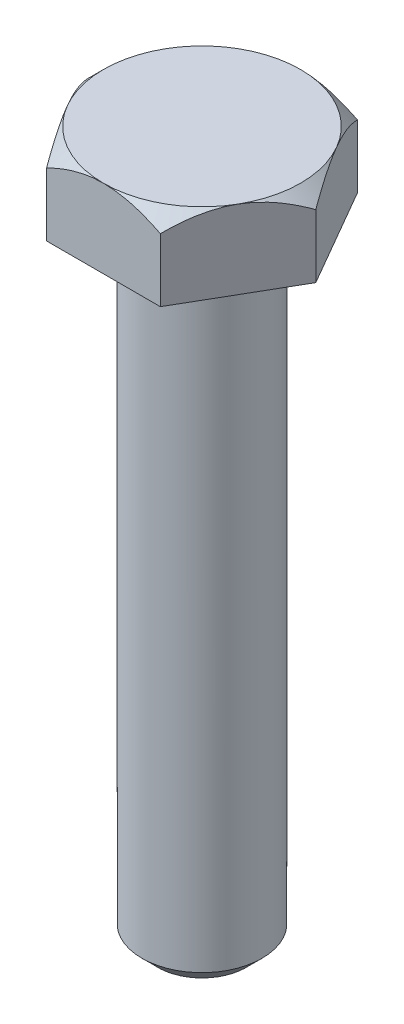
SolidWorks part; units mm, degrees
ref_plane "Спереди" through (0, 0, 0) normal (0, 0, 1) x (1, 0, 0)
ref_plane "Сверху" through (0, 0, 0) normal (0, 1, 0) x (1, 0, 0)
ref_plane "Справа" through (0, 0, 0) normal (1, 0, 0) x (0, 0, -1)
sketch "Эскиз6" plane through (0, 0, 0) normal (0, 1, 0) x (1, 0, 0)
  line L1 (7.25, 0) -> (3.625, 6.2787)
  line L2 (3.625, 6.2787) -> (-3.625, 6.2787)
  line L3 (-3.625, 6.2787) -> (-7.25, 0)
  line L4 (-7.25, 0) -> (-3.625, -6.2787)
  line L5 (-3.625, -6.2787) -> (3.625, -6.2787)
  line L6 (3.625, -6.2787) -> (7.25, 0)
  circle A0 centre (0, 0) radius 6.2787 construction
  dimension "D1" = 14.5
extrude "Бобышка-Вытянуть1" add sketch "Эскиз6" along normal blind 5
sketch "Эскиз8" plane through (0, 5, 0) normal (0, 1, 0) x (1, 0, 0)
  circle A0 centre (0, 0) radius 6.2787
extrude "Вырез-Вытянуть1" cut sketch "Эскиз8" against normal blind 1 draft 45 flip side to cut
sketch "Эскиз9" plane through (0, 0, 0) normal (0, -1, 0) x (1, 0, 0)
  circle A0 centre (0, 0) radius 3.825
  dimension "D1" = 7.65
extrude "bolt length" add sketch "Эскиз9" along normal blind 40
fillet "Скругление1" radius 1 1 edges at (0, 0, 3.825)
chamfer "Фаска1" distance 1 angle 45 1 edges at (0, -40, -3.825)
